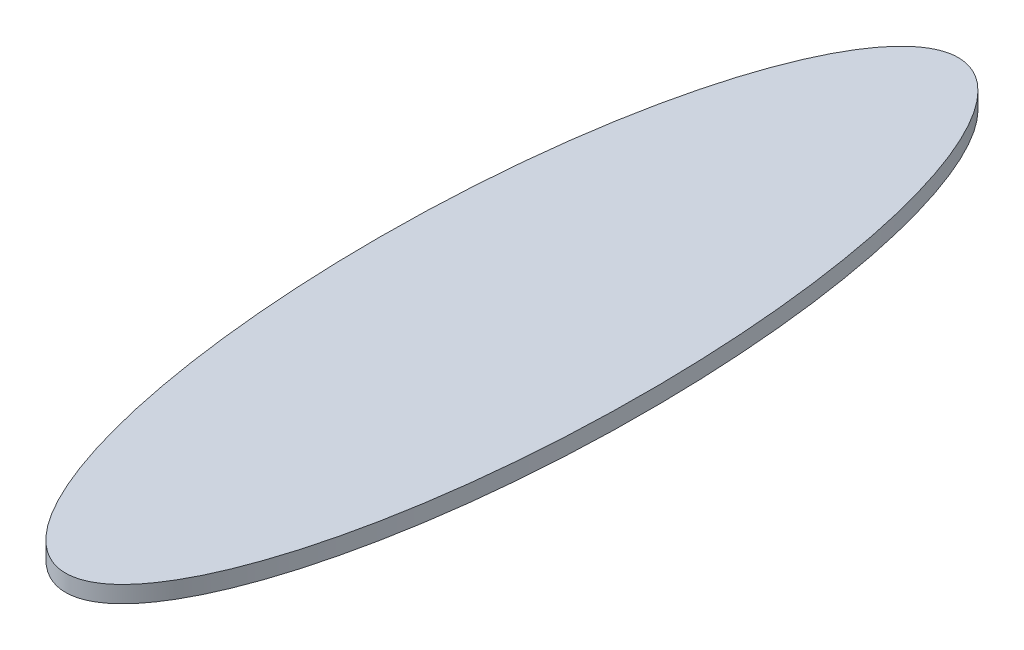
SolidWorks part; units mm, degrees
ref_plane "Front Plane" through (0, 0, 0) normal (0, 0, 1) x (1, 0, 0)
ref_plane "Top Plane" through (0, 0, 0) normal (0, 1, 0) x (1, 0, 0)
ref_plane "Right Plane" through (0, 0, 0) normal (1, 0, 0) x (0, 0, -1)
sketch "Sketch1" plane through (0, 0, 0) normal (0, 1, 0) x (1, 0, 0)
  ellipse E0 centre (0, 0) end of major axis (0, 127) minor radius 38.1
  dimension "D1" = 127
extrude "Boss-Extrude1" add sketch "Sketch1" along normal blind 4.7625 contours E0
